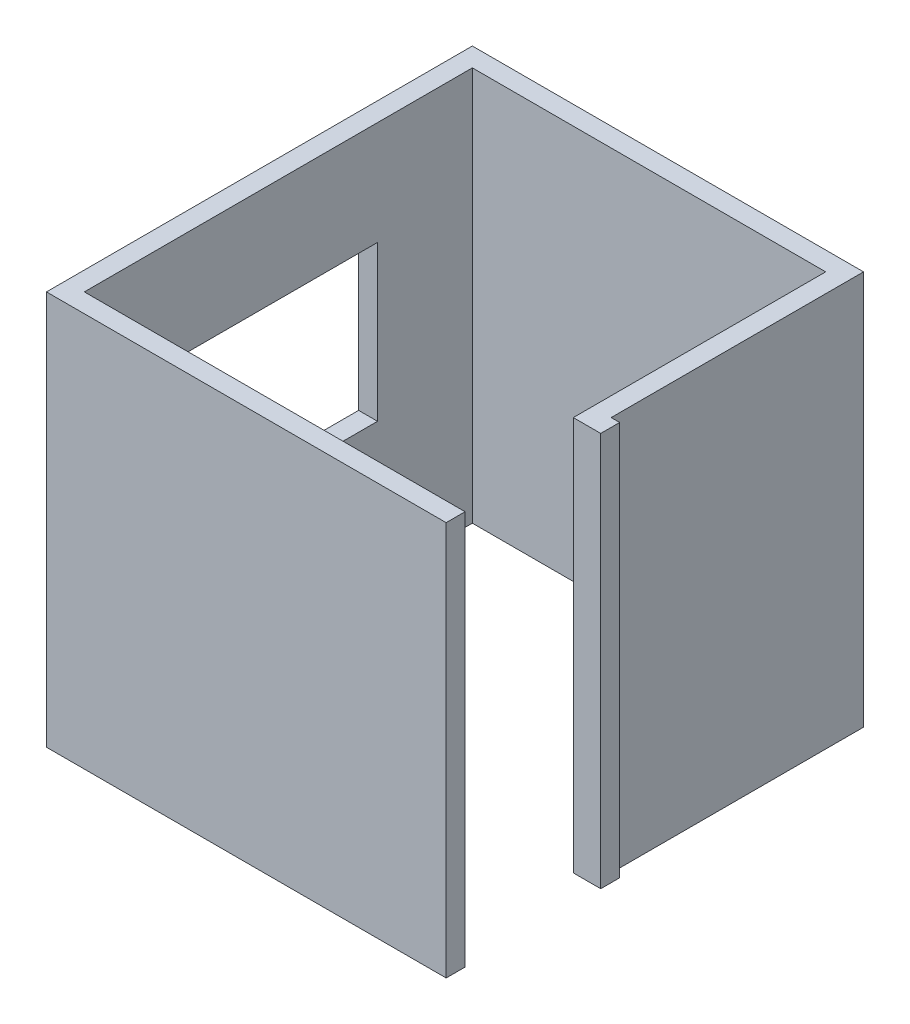
SolidWorks part; units mm, degrees
ref_plane "Спереди" through (0, 0, 0) normal (0, 0, 1) x (1, 0, 0)
ref_plane "Сверху" through (0, 0, 0) normal (0, 1, 0) x (1, 0, 0)
ref_plane "Справа" through (0, 0, 0) normal (1, 0, 0) x (0, 0, -1)
sketch "Эскиз1" plane through (0, 0, 0) normal (0, 1, 0) x (1, 0, 0)
  line L0 (0, 0) -> (0, 2460)
  line L1 (0, 2460) -> (2240, 2460)
  line L2 (2240, 2460) -> (2240, 860)
  line L3 (2240, 860) -> (2413.9408, 860)
  line L4 (0, 0) -> (2413.9408, 0)
  dimension "D1" = 1600
  dimension "D2" = 2460
  dimension "D3" = 2240
extrude "Вытянуть-Тонкостенный1" add sketch "Эскиз1" along normal blind 2500 thin thin type one direction wall 120
sketch "Эскиз2" plane through (-120, 0, 0) normal (-1, 0, 0) x (0, 0, 1)
  line L1 (-1859, 1842.1461) -> (-489, 1842.1461)
  line L2 (-1859, 1842.1461) -> (-1859, 860)
  line L3 (-1859, 860) -> (-489, 860)
  line L4 (-489, 1842.1461) -> (-489, 860)
extrude "Вырез-Вытянуть1" cut sketch "Эскиз2" against normal up to next
